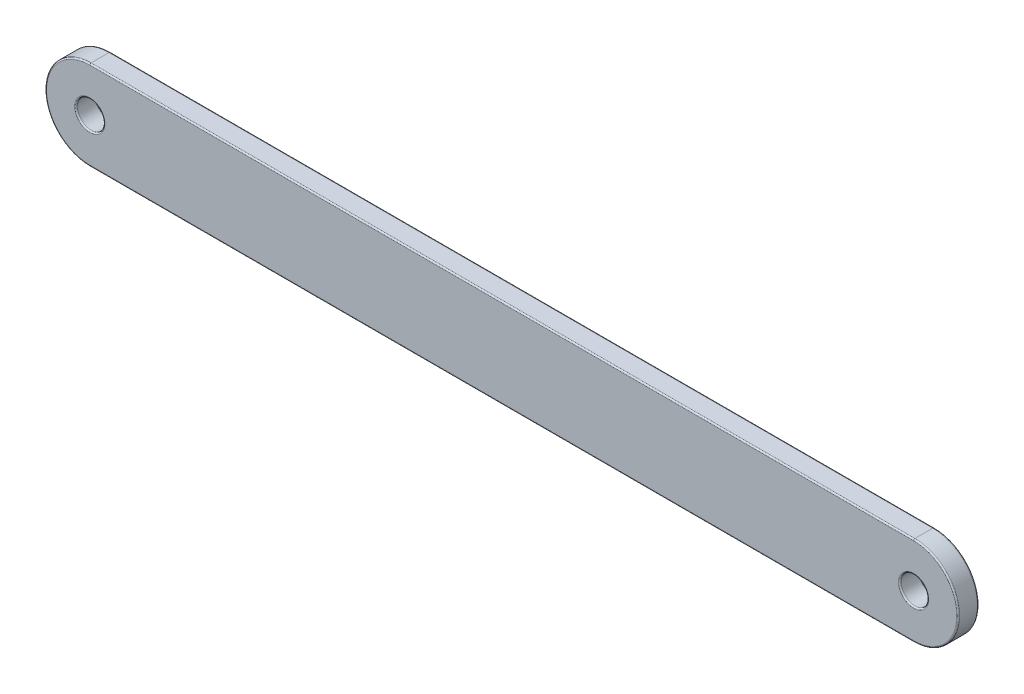
SolidWorks part; units mm, degrees
ref_plane "Front Plane" through (0, 0, 0) normal (0, 0, 1) x (1, 0, 0)
ref_plane "Top Plane" through (0, 0, 0) normal (0, 1, 0) x (1, 0, 0)
ref_plane "Right Plane" through (0, 0, 0) normal (1, 0, 0) x (0, 0, -1)
sketch "Sketch1" plane through (0, 0, 0) normal (0, 0, 1) x (1, 0, 0)
  line L0 (-30, 0) -> (30, 0) construction
  line L1 (-30, 3.25) -> (30, 3.25)
  line L2 (-30, -3.25) -> (30, -3.25)
  arc A0 (-30, 3.25) -> (-30, -3.25) centre (-30, 0) ccw
  arc A1 (30, -3.25) -> (30, 3.25) centre (30, 0) ccw
  circle A2 centre (-30, 0) radius 1
  circle A3 centre (30, 0) radius 1
  point P3 (0, 0)
  dimension "D1" = 3.25
  dimension "D3" = 2
  dimension "D2" = 60
extrude "Boss-Extrude1" add sketch "Sketch1" along normal blind 1.5
fillet "Fillet1" radius 0.1 12 edges at (31, 0, 0) (31, 0, 1.5) (-29, 0, 0) (-29, 0, 1.5) (-33.25, 0, 0) (0, -3.25, 0) (33.25, 0, 0) (0, 3.25, 0) (-33.25, 0, 1.5) (0, -3.25, 1.5) (33.25, 0, 1.5) (0, 3.25, 1.5)
